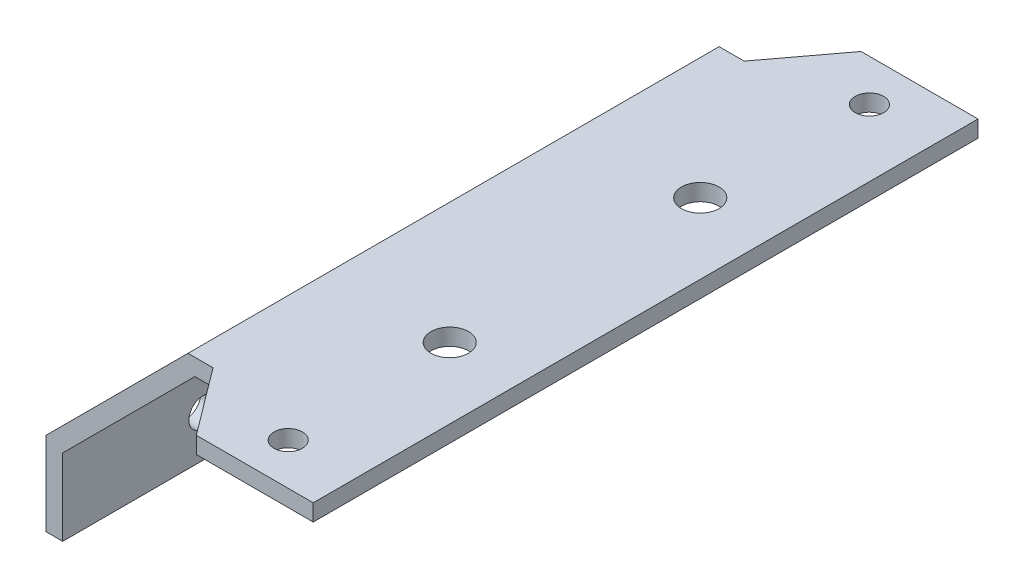
SolidWorks part; units mm, degrees
ref_plane "Front Plane" through (0, 0, 0) normal (0, 0, 1) x (1, 0, 0)
ref_plane "Top Plane" through (0, 0, 0) normal (0, 1, 0) x (1, 0, 0)
ref_plane "Right Plane" through (0, 0, 0) normal (1, 0, 0) x (0, 0, -1)
sketch "Sketch1" plane through (0, 0, 0) normal (0, 0, 1) x (1, 0, 0)
  line L0 (0, 0) -> (0, 9.1716)
  line L1 (0, 9.1716) -> (15.8284, 25)
  line L2 (15.8284, 25) -> (38, 25)
  line L3 (38, 25) -> (38, 27)
  line L4 (38, 27) -> (15, 27)
  line L5 (15, 27) -> (-2, 10)
  line L6 (-2, 10) -> (-2, 0)
  line L7 (-2, 0) -> (0, 0)
  dimension "D1" = 2
  dimension "D2" = 2
  dimension "D3" = 2
  dimension "D4" = 17
  dimension "D5" = 40
  dimension "D6" = 135
  dimension "D7" = 10
extrude "Boss-Extrude1" add sketch "Sketch1" along normal mid plane 63.6
hole_wizard "M3 Clearance Hole1" positions "Sketch2" profile "Sketch3" hole size "M3" standard "ANSI Metric"
sketch "Sketch2" plane through (0, 0, 0) normal (1, 0, 0) x (0, 0, -1)
  line L0 (-31.8, 0) -> (31.8, 0) construction
  point P0 (5, 5)
  point P2 (-5, 5)
  point P4 (-15, 5)
  point P6 (15, 5)
  dimension "D1" = 10
  dimension "D2" = 10
  dimension "D3" = 10
  dimension "D4" = 5
  dimension "D5" = 5
sketch "Sketch3" plane through (0, 5, -5) normal (0, 1, 0) x (0, 0, -1)
  line L0 (0, 0) -> (0, 6.0215)
  line L1 (0, 6.0215) -> (1.7, 5)
  line L2 (1.7, 5) -> (1.7, 0)
  line L5 (1.7, 0) -> (0, 0)
  line L10 (0, 6.0215) -> (-1.7, 5) construction
  line L11 (0, -6.35) -> (0, 107.95) construction
  dimension "Hole Dia." = 3.4
  dimension "Hole Depth" = 5
  dimension "Drill Angle" = 118
sketch "Sketch4" plane through (0, 27, 0) normal (0, 1, 0) x (1, 0, 0)
  line L0 (18, -31.8) -> (24, -39.8)
  line L1 (24, -39.8) -> (38, -39.8)
  line L2 (38, -39.8) -> (38, -31.8)
  line L4 (38, -31.8) -> (15, -31.8) construction
  line L5 (18, -31.8) -> (38, -31.8)
  dimension "D1" = 8
  dimension "D2" = 14
  dimension "D3" = 20
extrude "Boss-Extrude2" add sketch "Sketch4" against normal blind 2 contours L0 L1 L2 L5
mirror "Mirror1" about plane through (0, 0, 0) normal (0, 0, 1) of "Boss-Extrude2"
hole_wizard "M3 Clearance Hole2" positions "Sketch5" profile "Sketch6" hole size "M3" standard "ANSI Metric"
sketch "Sketch5" plane through (0, 27, 0) normal (0, 1, 0) x (1, 0, 0)
  line L0 (30, 34.8) -> (30, -34.8) construction
  line L2 (-2, -31.8) -> (-2, 31.8) construction
  point P0 (30, 34.8)
  point P2 (30, -34.8)
  point P15 (30, 0)
  dimension "D1" = 69.6
  dimension "D2" = 32
sketch "Sketch6" plane through (30, 27, -34.8) normal (1, 0, 0) x (0, 0, 1)
  line L0 (0, 0) -> (0, 6.0215)
  line L1 (0, 6.0215) -> (1.7, 5)
  line L2 (1.7, 5) -> (1.7, 0)
  line L5 (1.7, 0) -> (0, 0)
  line L10 (0, 6.0215) -> (-1.7, 5) construction
  line L11 (0, -6.35) -> (0, 107.95) construction
  dimension "Hole Dia." = 3.4
  dimension "Hole Depth" = 5
  dimension "Drill Angle" = 118
hole_wizard "M4 Clearance Hole1" positions "Sketch7" profile "Sketch8" hole size "M4" standard "ANSI Metric" end condition through all
sketch "Sketch7" plane through (0, 25, 0) normal (0, -1, 0) x (-1, 0, 0)
  point P0 (-29.5415, 15)
  point P4 (-29.5415, -15)
  point P7 (0, 0)
  point P8 (0, 0)
  point P9 (0, 0)
  point P12 (0, 0)
  point P13 (0, 0)
  point P19 (-34.9172, -1.8373)
  point P22 (-29.5415, 15)
  point P23 (0, 0)
  dimension "D1" = 15
  dimension "D2" = 30
sketch "Sketch8" plane through (29.5415, 25, -15) normal (1, 0, 0) x (0, 0, -1)
  line L0 (0, 0) -> (0, 2)
  line L1 (0, 2) -> (2.25, 2)
  line L2 (2.25, 2) -> (2.25, 0)
  line L5 (2.25, 0) -> (0, 0)
  line L11 (0, -6.35) -> (0, 107.95) construction
  dimension "Thru Hole Dia." = 4.5
  dimension "Thru Hole Depth" = 2
